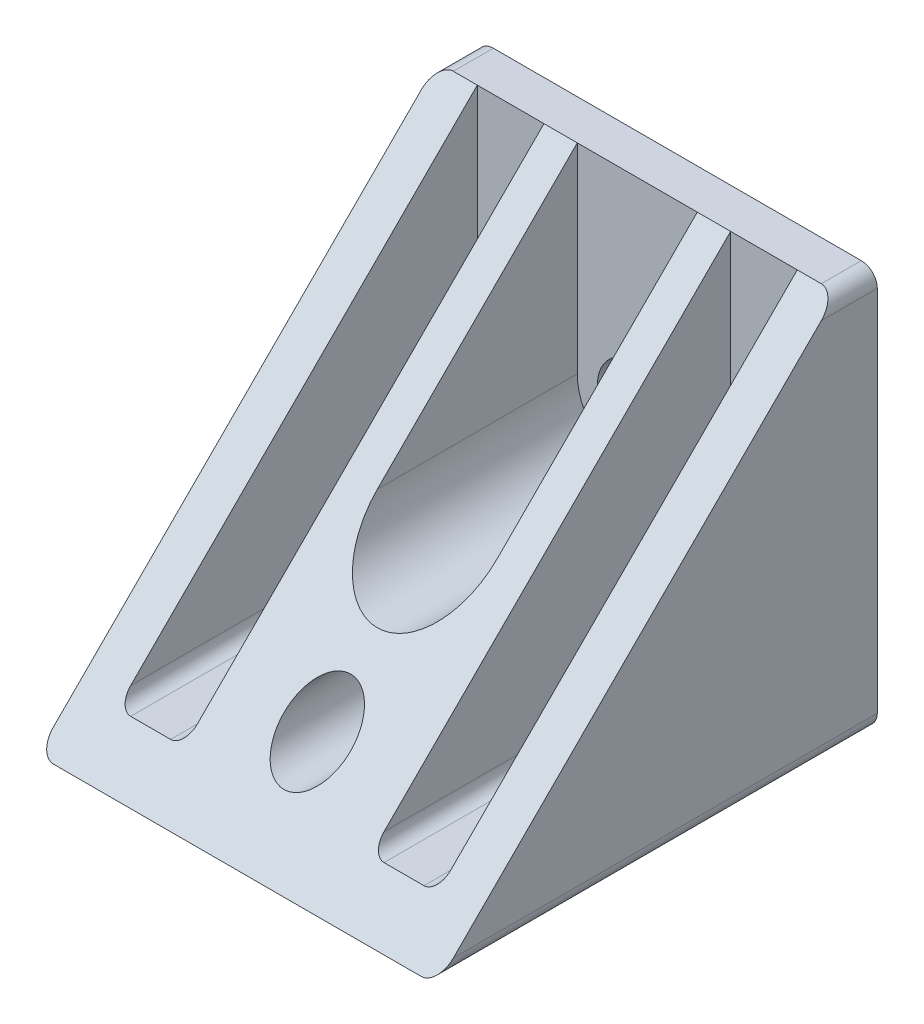
SolidWorks part; units mm, degrees
material "201 退火不锈钢 (SS)"
ref_plane "前视基准面" through (0, 0, 0) normal (0, 0, 1) x (1, 0, 0)
ref_plane "上视基准面" through (0, 0, 0) normal (0, 1, 0) x (1, 0, 0)
ref_plane "右视基准面" through (0, 0, 0) normal (1, 0, 0) x (0, 0, -1)
sketch "草图1" plane through (0, 0, 0) normal (1, 0, 0) x (0, 0, -1)
  line L0 (0, 30) -> (0, 0)
  line L1 (0, 0) -> (-33, 0)
  line L2 (-33, 0) -> (-3, 30)
  line L3 (-3, 30) -> (0, 30)
  dimension "D1" = 33
  dimension "D2" = 30
  dimension "D3" = 3
extrude "凸台-拉伸1" add sketch "草图1" along normal blind 30
ref_plane "基准面1" through (0, 0, 3) normal (0, 0, -1) x (-1, 0, 0)
sketch "草图2" plane through (0, 0, 3) normal (0, 0, -1) x (-1, 0, 0)
  line L0 (-15, 15) -> (-15, 31.773) construction
  line L1 (-19.5, 15) -> (-19.5, 31.773)
  line L2 (-10.5, 15) -> (-10.5, 31.773)
  line L3 (-30, 30) -> (-30, 0) construction
  line L4 (-30, 30) -> (0, 30) construction
  line L5 (-3, 57) -> (-8, 57)
  line L6 (-3, 57) -> (-3, 3)
  line L7 (-3, 3) -> (-8, 3)
  line L8 (-8, 57) -> (-8, 3)
  line L9 (-3, 57) -> (-8, 3) construction
  line L10 (-3, 3) -> (-8, 57) construction
  line L11 (0, 30) -> (0, 0) construction
  line L12 (-22, 57) -> (-27, 57)
  line L13 (-22, 57) -> (-22, 3)
  line L14 (-22, 3) -> (-27, 3)
  line L15 (-27, 57) -> (-27, 3)
  line L16 (-22, 57) -> (-27, 3) construction
  line L17 (-22, 3) -> (-27, 57) construction
  line L18 (-30, 0) -> (0, 0) construction
  arc A0 (-19.5, 15) -> (-10.5, 15) centre (-15, 15) ccw
  arc A1 (-10.5, 31.773) -> (-19.5, 31.773) centre (-15, 31.773) ccw
  point P2 (-15, 23.3865)
  point P9 (-5.5, 30)
  point P16 (-24.5, 30)
  dimension "D1" = 4.5
  dimension "D2" = 15
  dimension "D3" = 5
  dimension "D4" = 5
  dimension "D5" = 3
  dimension "D6" = 3
  dimension "D7" = 3
  dimension "D8" = 3
  dimension "D9" = 15
extrude "切除-拉伸1" cut sketch "草图2" against normal blind 45
fillet "圆角1" radius 1 4 edges at (8, 3, 16.5) (3, 3, 16.5) (22, 3, 16.5) (27, 3, 16.5)
sketch "草图4" plane through (0, 0, 3) normal (0, 0, 1) x (1, 0, 0)
  circle A0 centre (15, 15) radius 3
  dimension "D1" = 6
extrude "切除-拉伸2" cut sketch "草图4" against normal blind 45
sketch "草图5" plane through (0, 0, 0) normal (0, 0, 1) x (1, 0, 0)
  line L0 (30, 30) -> (30, 0) construction
  line L1 (30, 0) -> (0, 0) construction
  circle A0 centre (15, 6) radius 2.5
  dimension "D1" = 15
  dimension "D2" = 6
  dimension "D3" = 5
extrude "切除-拉伸3" cut sketch "草图5" along normal blind 92
fillet "圆角2" radius 1.2 4 edges at (30, 30, 1.5) (30, 0, 16.5) (0, 0, 16.5) (0, 30, 1.5)
